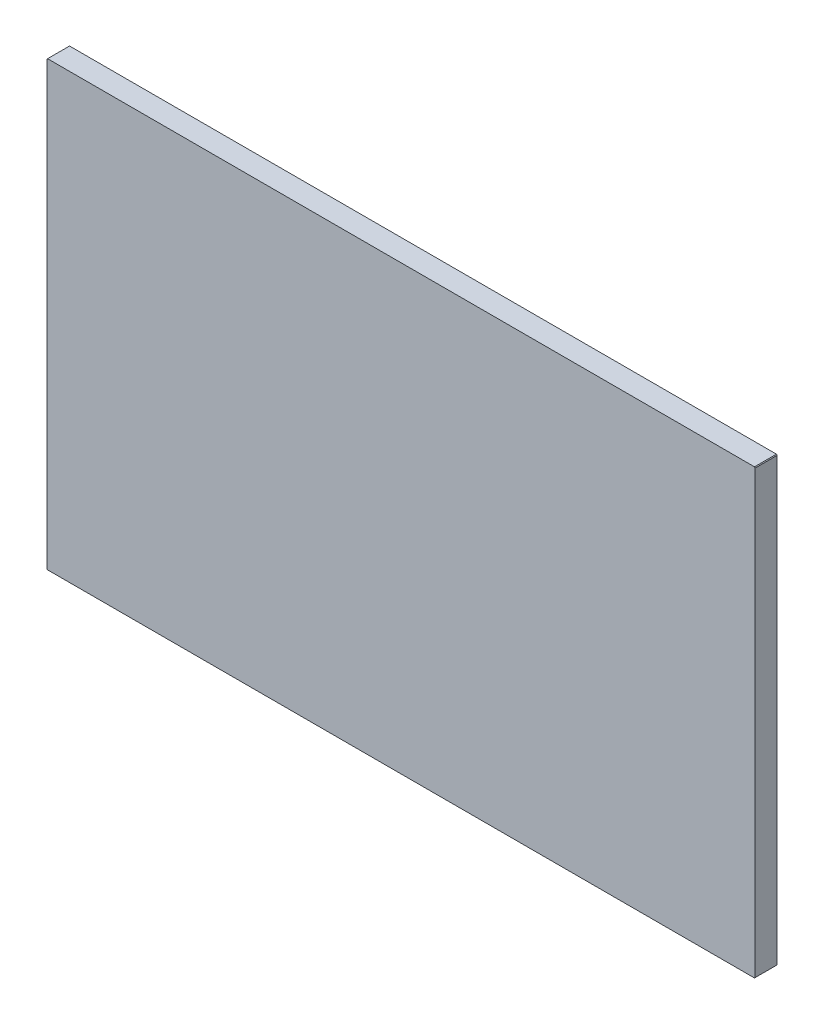
SolidWorks part; units mm, degrees
material "302 SSTL"
ref_plane "Front" through (0, 0, 0) normal (0, 0, 1) x (1, 0, 0)
ref_plane "Top" through (0, 0, 0) normal (0, 1, 0) x (1, 0, 0)
ref_plane "Right" through (0, 0, 0) normal (1, 0, 0) x (0, 0, -1)
sketch "Sketch1" plane through (0, 0, 0) normal (0, 0, 1) x (1, 0, 0)
  line L0 (-25.3746, 15.875) -> (-25.4, 15.8496)
  line L1 (-0.0254, 0) -> (-25.3746, 0)
  line L2 (0, 0.0254) -> (0, 15.8496)
  line L3 (-0.0254, 15.875) -> (-25.3746, 15.875)
  line L4 (-25.4, 0.0254) -> (-25.4, 15.8496)
  line L5 (-25.3746, 0) -> (-25.4, 0.0254)
  line L6 (0, 0.0254) -> (-0.0254, 0)
  line L7 (0, 15.8496) -> (-0.0254, 15.875)
  point P9 (-25.4, 15.875)
  point P12 (-25.4, 0)
  point P15 (0, 15.875)
  point P18 (0, 0)
  point P19 (-25.4, 15.875)
  point P22 (-25.4, 0)
  point P25 (0, 0)
  point P28 (0, 15.875)
  dimension "D1" = 15.875
  dimension "D2" = 25.4
  dimension "D7" = 0.0254
  dimension "D8" = 0.0254
  dimension "D9" = 0.0254
  dimension "D10" = 0.0254
extrude "Extrude1" add sketch "Sketch1" along normal blind 0.7874
